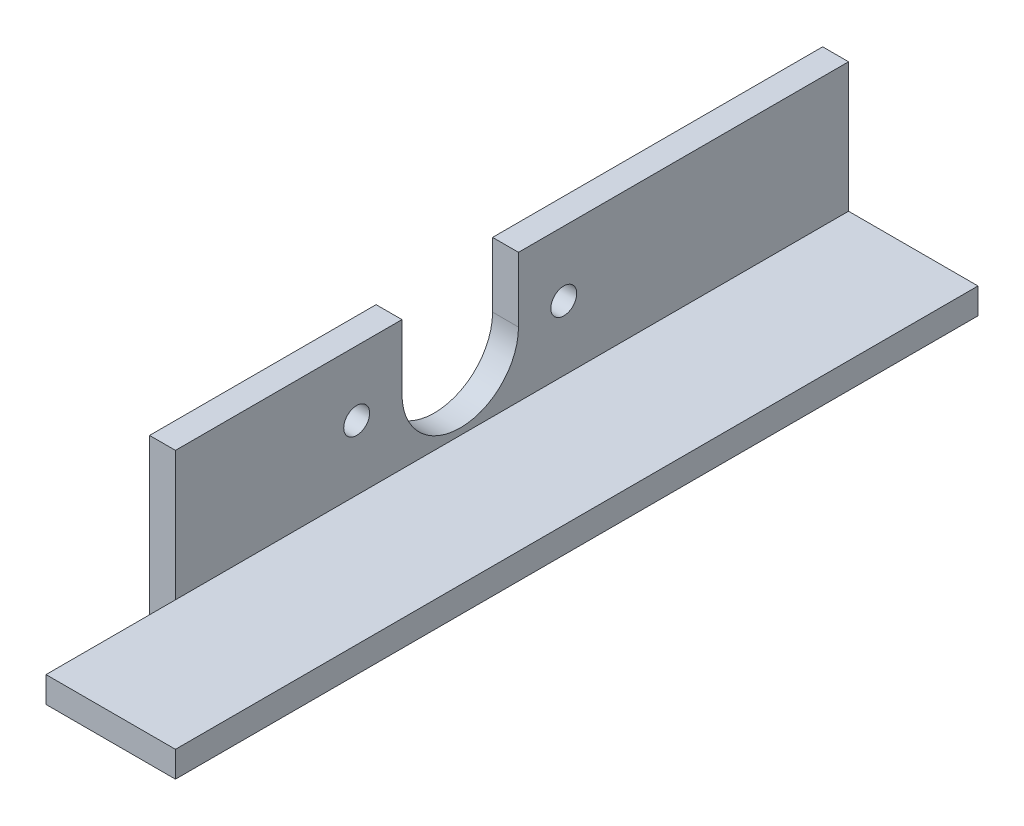
SolidWorks part; units mm, degrees
ref_plane "Front Plane" through (0, 0, 0) normal (0, 0, 1) x (1, 0, 0)
ref_plane "Top Plane" through (0, 0, 0) normal (0, 1, 0) x (1, 0, 0)
ref_plane "Right Plane" through (0, 0, 0) normal (1, 0, 0) x (0, 0, -1)
sketch "Sketch1" plane through (0, 0, 0) normal (0, 0, 1) x (1, 0, 0)
  line L0 (0, 0) -> (0, 38.1)
  line L1 (0, 38.1) -> (6.35, 38.1)
  line L2 (6.35, 38.1) -> (6.35, 6.35)
  line L3 (6.35, 6.35) -> (0, 0) construction
  line L4 (38.1, 6.35) -> (6.35, 6.35)
  line L5 (38.1, 0) -> (38.1, 6.35)
  line L6 (0, 0) -> (38.1, 0)
  dimension "D1" = 38.1
  dimension "D2" = 6.35
  dimension "D3" = 45
extrude "Boss-Extrude1" add sketch "Sketch1" along normal blind 196.85
sketch "Sketch2" plane through (0, 0, 0) normal (1, 0, 0) x (0, 0, -1)
  line L1 (-196.85, 38.1) -> (-165.1, 38.1)
  line L2 (-196.85, 38.1) -> (-196.85, 0)
  line L3 (-196.85, 0) -> (-165.1, 0)
  line L4 (-165.1, 38.1) -> (-165.1, 0)
  line L5 (-196.85, 0) -> (0, 0) construction
  dimension "D1" = 31.75
extrude "Cut-Extrude1" cut sketch "Sketch2" along normal blind 6.35
sketch "Sketch3" plane through (6.35, 0, 0) normal (1, 0, 0) x (0, 0, -1)
  line L0 (-95.25, -3.175) -> (-95.25, 22.225) construction
  line L1 (-165.1, 38.1) -> (0, 38.1) construction
  line L2 (-196.85, 0) -> (-196.85, 6.35) construction
  line L4 (-109.5375, 22.225) -> (-109.5375, 38.1)
  line L6 (-80.9625, 22.225) -> (-80.9625, 38.1)
  line L8 (-80.9625, 38.1) -> (-109.5375, 38.1)
  line L10 (-95.25, 22.225) -> (-120.65, 22.225) construction
  line L11 (-120.65, 22.225) -> (-120.65, 38.1) construction
  circle A0 centre (-95.25, 22.225) radius 14.2875 construction
  circle A1 centre (-120.65, 22.225) radius 3.175
  circle A2 centre (-69.85, 22.225) radius 3.175
  arc A3 (-109.5375, 22.225) -> (-80.9625, 22.225) centre (-95.25, 22.225) ccw
  dimension "D1" = 28.575
  dimension "D5" = 6.35
  dimension "D2" = 25.4
  dimension "D3" = 25.4
  dimension "D4" = 15.875
  dimension "D6" = 101.6
  dimension "D7" = 15.875
extrude "Cut-Extrude2" cut sketch "Sketch3" against normal through all
